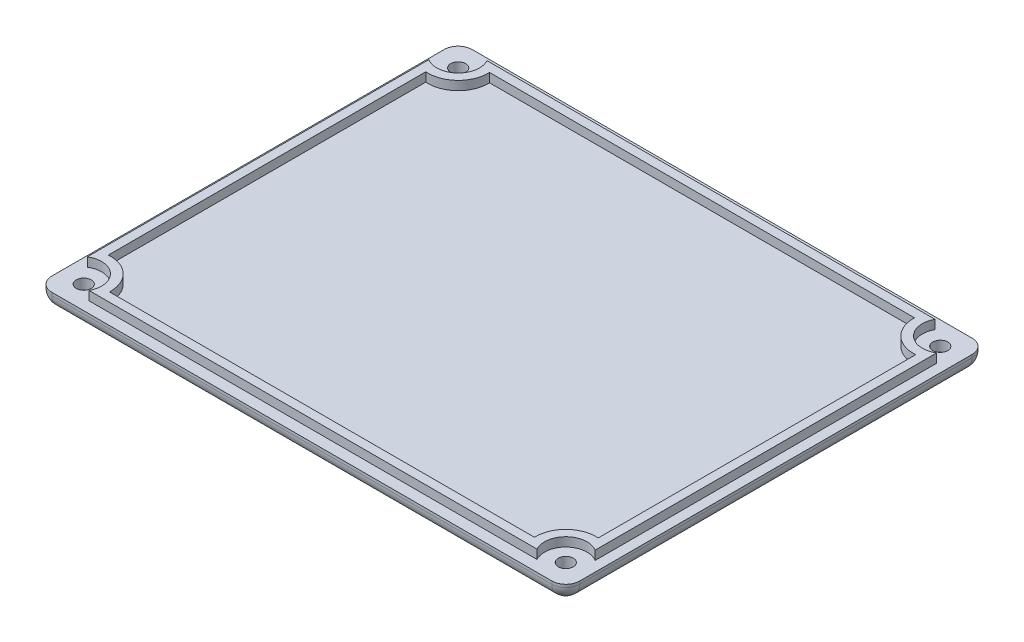
SolidWorks part; units mm, degrees
ref_plane "Front Plane" through (0, 0, 0) normal (0, 0, 1) x (1, 0, 0)
ref_plane "Top Plane" through (0, 0, 0) normal (0, 1, 0) x (1, 0, 0)
ref_plane "Right Plane" through (0, 0, 0) normal (1, 0, 0) x (0, 0, -1)
sketch "Sketch1" plane through (0, 0, 0) normal (0, 1, 0) x (1, 0, 0)
  line L1 (0, 0) -> (119.634, 0)
  line L2 (0, 0) -> (0, 95.25)
  line L3 (0, 95.25) -> (119.634, 95.25)
  line L4 (119.634, 0) -> (119.634, 95.25)
  dimension "D1" = 119.634
  dimension "D2" = 95.25
extrude "Boss-Extrude1" add sketch "Sketch1" along normal blind 3.81
fillet "Fillet1" radius 3.175 8 edges at (59.817, 0, 0) (119.634, 0, -47.625) (59.817, 0, -95.25) (0, 0, -47.625) (0, 1.905, -95.25) (0, 1.905, 0) (119.634, 1.905, -95.25) (119.634, 1.905, 0)
sketch "Sketch2" plane through (0, 3.81, 0) normal (0, 1, 0) x (1, 0, 0)
  line L0 (0, 92.075) -> (0, 3.175) construction
  line L1 (9.0762, 92.71) -> (110.5578, 92.71)
  line L2 (2.286, 86.3205) -> (2.286, 8.9295)
  line L3 (9.0762, 2.54) -> (110.5578, 2.54)
  line L4 (117.348, 86.3205) -> (117.348, 8.9295)
  line L5 (3.175, 0) -> (116.459, 0) construction
  line L6 (119.634, 3.175) -> (119.634, 92.075) construction
  line L7 (11.6793, 90.678) -> (107.9547, 90.678)
  line L8 (115.316, 83.5848) -> (115.316, 11.6652)
  line L9 (116.459, 95.25) -> (3.175, 95.25) construction
  line L10 (11.6793, 4.572) -> (107.9547, 4.572)
  line L11 (4.318, 83.5848) -> (4.318, 11.6652)
  arc A0 (9.0762, 92.71) -> (2.286, 86.3205) centre (4.826, 90.424) cw
  arc A1 (110.5578, 92.71) -> (117.348, 86.3205) centre (114.808, 90.424) ccw
  arc A2 (117.348, 8.9295) -> (110.5578, 2.54) centre (114.808, 4.826) ccw
  arc A3 (9.0762, 2.54) -> (2.286, 8.9295) centre (4.826, 4.826) ccw
  arc A4 (107.9547, 90.678) -> (115.316, 83.5848) centre (114.808, 90.424) ccw
  arc A5 (115.316, 11.6652) -> (107.9547, 4.572) centre (114.808, 4.826) ccw
  arc A6 (11.6793, 4.572) -> (4.318, 11.6652) centre (4.826, 4.826) ccw
  arc A7 (11.6793, 90.678) -> (4.318, 83.5848) centre (4.826, 90.424) cw
  point P23 (0, 21.3471)
  dimension "D7" = 4.826
  dimension "D14" = 4.826
  dimension "D10" = 4.826
  dimension "D13" = 4.826
  dimension "D16" = 4.826
  dimension "D1" = 2.286
  dimension "D2" = 2.54
  dimension "D3" = 115.062
  dimension "D4" = 90.17
  dimension "D5" = 4.826
  dimension "D6" = 4.826
  dimension "D8" = 4.826
  dimension "D9" = 4.826
  dimension "D11" = 4.826
  dimension "D12" = 4.826
  dimension "D15" = 4.826
  dimension "D17" = 2.032
extrude "Boss-Extrude2" add sketch "Sketch2" along normal blind 2.032
hole_wizard "CSK for M3 Flat Head Machine Screw1" positions "Sketch4" profile "Sketch5" countersink size "M3" standard "ANSI Metric"
sketch "Sketch4" plane through (0, 0, 0) normal (0, -1, 0) x (-1, 0, 0)
  line L4 (-116.459, 95.25) -> (-3.175, 95.25) construction
  line L5 (0, 92.075) -> (0, 3.175) construction
  line L6 (0, 47.625) -> (-119.634, 47.625) construction
  line L7 (-119.634, 3.175) -> (-119.634, 92.075) construction
  line L9 (-59.817, 95.25) -> (-59.817, 0) construction
  line L10 (-3.175, 0) -> (-116.459, 0) construction
  point P0 (-114.427, 5.207)
  point P2 (-5.207, 5.207)
  point P4 (-5.207, 90.043)
  point P6 (-114.427, 90.043)
  dimension "D1" = 84.836
  dimension "D2" = 109.22
sketch "Sketch5" plane through (114.427, 0, -5.207) normal (1, 0, 0) x (0, 0, -1)
  line L0 (0, 0) -> (0, 26.4215)
  line L1 (0, 26.4215) -> (1.7, 25.4)
  line L2 (1.7, 25.4) -> (1.7, 1.45)
  line L3 (1.7, 1.45) -> (3.15, 0)
  line L5 (3.15, 0) -> (0, 0)
  line L6 (-1.7, 1.45) -> (-3.15, 0) construction
  line L10 (0, 26.4215) -> (-1.7, 25.4) construction
  line L11 (0, -6.35) -> (0, 107.95) construction
  dimension "Hole Dia." = 3.4
  dimension "Hole Depth" = 25.4
  dimension "Near C'Sink Dia." = 6.3
  dimension "Near C'Sink Angle" = 90
  dimension "Drill Angle" = 118
